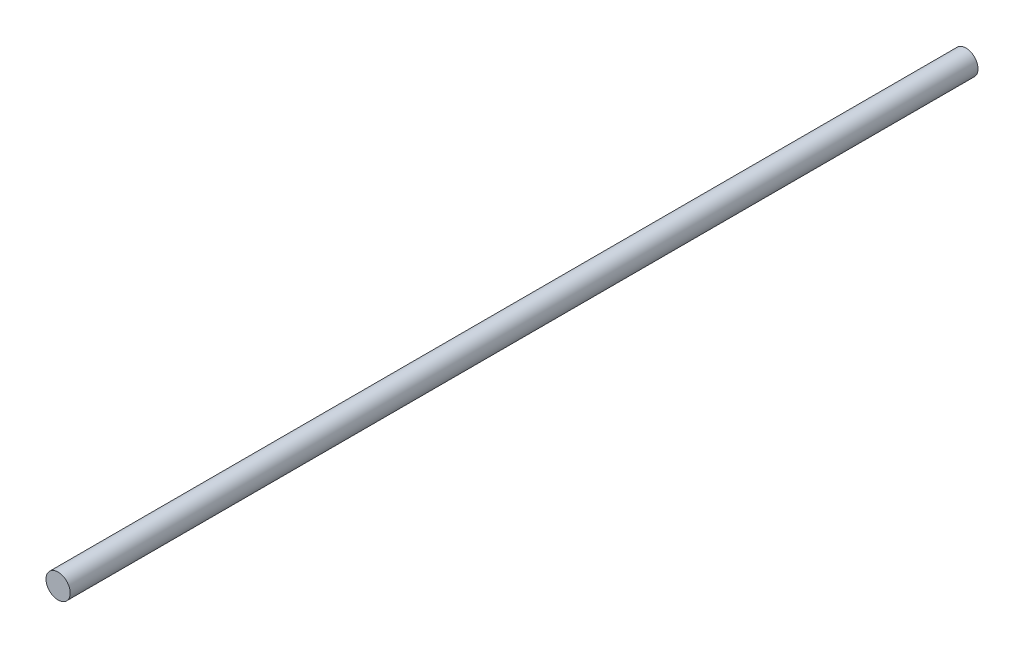
SolidWorks part; units mm, degrees
ref_plane "Front Plane" through (0, 0, 0) normal (0, 0, 1) x (1, 0, 0)
ref_plane "Top Plane" through (0, 0, 0) normal (0, 1, 0) x (1, 0, 0)
ref_plane "Right Plane" through (0, 0, 0) normal (1, 0, 0) x (0, 0, -1)
sketch "Sketch1" plane through (0, 0, 0) normal (0, 0, 1) x (1, 0, 0)
  circle A0 centre (-3.9625, 1.9301) radius 4
  dimension "D1" = 8
extrude "Boss-Extrude1" add sketch "Sketch1" along normal blind 300
